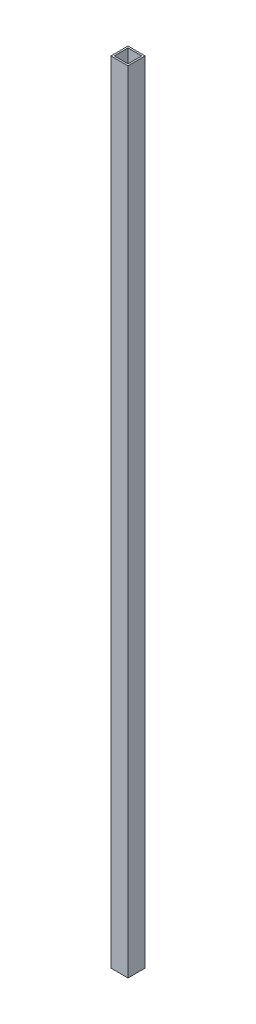
SolidWorks part; units mm, degrees
ref_plane "Front Plane" through (0, 0, 0) normal (0, 0, 1) x (1, 0, 0)
ref_plane "Top Plane" through (0, 0, 0) normal (0, 1, 0) x (1, 0, 0)
ref_plane "Right Plane" through (0, 0, 0) normal (1, 0, 0) x (0, 0, -1)
sketch "Sketch2" plane through (0, 0, 0) normal (0, 0, 1) x (1, 0, 0)
  line L0 (0, 0) -> (0, 1168.4)
  dimension "D1" = 1168.4
other "Extrusion 1X1X0.1(1)"
ref_plane "Plane3" through (0, 0, 0) normal (0, 1, 0) x (-1, 0, 0)
sketch "Sketch1" plane through (0, 0, 0) normal (0, 1, 0) x (-1, 0, 0)
  line L0 (22.86, 2.54) -> (22.86, 22.86)
  line L1 (0, 0) -> (25.4, 0)
  line L2 (0, 0) -> (0, 25.4)
  line L3 (0, 25.4) -> (25.4, 25.4)
  line L4 (25.4, 0) -> (25.4, 25.4)
  line L5 (2.54, 22.86) -> (22.86, 22.86)
  line L6 (2.54, 2.54) -> (2.54, 22.86)
  line L7 (2.54, 2.54) -> (22.86, 2.54)
  line L8 (12.7, 0) -> (12.7, 25.4) construction
  point P8 (25.4, 12.7)
  point P9 (0, 25.4)
  point P10 (25.4, 25.4)
  point P11 (0, 12.7)
  point P12 (12.7, 0)
  point P13 (0, 0)
  point P15 (25.4, 0)
  point P17 (12.7, 12.7)
  point P18 (0, 0)
  dimension "D1" = 25.4
  dimension "D2" = 25.4
  dimension "D3" = 2.54
